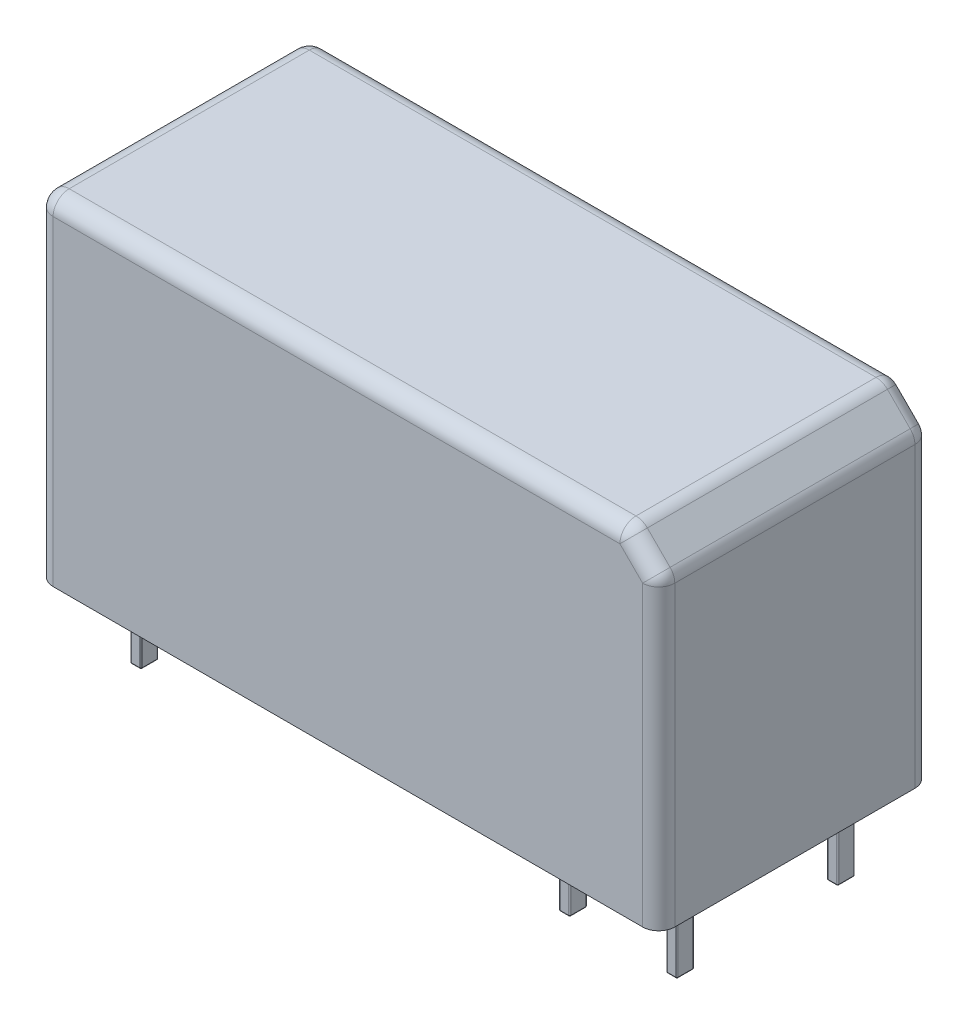
SolidWorks part; units mm, degrees
ref_plane "Спереди" through (0, 0, 0) normal (0, 0, 1) x (1, 0, 0)
ref_plane "Сверху" through (0, 0, 0) normal (0, 1, 0) x (1, 0, 0)
ref_plane "Справа" through (0, 0, 0) normal (1, 0, 0) x (0, 0, -1)
sketch "Эскиз1" plane through (0, 0, 0) normal (0, 1, 0) x (1, 0, 0)
  line L1 (-14.5, -6.35) -> (14.5, -6.35)
  line L2 (-14.5, -6.35) -> (-14.5, 6.35)
  line L3 (-14.5, 6.35) -> (14.5, 6.35)
  line L4 (14.5, -6.35) -> (14.5, 6.35)
  line L5 (-14.5, -6.35) -> (14.5, 6.35) construction
  line L6 (-14.5, 6.35) -> (14.5, -6.35) construction
  point P0 (0, 0)
  dimension "D1" = 29
  dimension "D2" = 12.7
extrude "Бобышка-Вытянуть1" add sketch "Эскиз1" along normal blind 15.7
sketch "Эскиз2" plane through (0, 0, 0) normal (0, -1, 0) x (1, 0, 0)
  line L0 (-14.5, -6.35) -> (-14.5, 6.35) construction
  line L1 (-12.3, 4.15) -> (-11.9, 4.15)
  line L2 (-12.35, 4.1) -> (-12.35, 3.4)
  line L3 (-12.3, 3.35) -> (-11.9, 3.35)
  line L4 (-11.85, 4.1) -> (-11.85, 3.4)
  line L5 (-12.35, 4.15) -> (-11.85, 3.35) construction
  line L6 (-12.35, 3.35) -> (-11.85, 4.15) construction
  line L7 (-7.35, 4.1) -> (-7.35, 3.4) [skipped]
  line L8 (-6.85, 4.1) -> (-6.85, 3.4) [skipped]
  line L9 (-7.3, 4.15) -> (-6.9, 4.15) [skipped]
  line L10 (-7.3, 3.35) -> (-6.9, 3.35) [skipped]
  line L11 (-2.35, 4.1) -> (-2.35, 3.4) [skipped]
  line L12 (-1.85, 4.1) -> (-1.85, 3.4) [skipped]
  line L13 (-2.3, 4.15) -> (-1.9, 4.15) [skipped]
  line L14 (-2.3, 3.35) -> (-1.9, 3.35) [skipped]
  line L19 (7.65, 4.1) -> (7.65, 3.4)
  line L20 (8.15, 4.1) -> (8.15, 3.4)
  line L21 (7.7, 4.15) -> (8.1, 4.15)
  line L22 (7.7, 3.35) -> (8.1, 3.35)
  line L23 (12.65, 4.1) -> (12.65, 3.4)
  line L24 (13.15, 4.1) -> (13.15, 3.4)
  line L25 (12.7, 4.15) -> (13.1, 4.15)
  line L26 (12.7, 3.35) -> (13.1, 3.35)
  line L27 (-7.35, -3.4) -> (-7.35, -4.1) [skipped]
  line L28 (-6.85, -3.4) -> (-6.85, -4.1) [skipped]
  line L29 (-7.3, -3.35) -> (-6.9, -3.35) [skipped]
  line L30 (-7.3, -4.15) -> (-6.9, -4.15) [skipped]
  line L31 (-2.35, -3.4) -> (-2.35, -4.1) [skipped]
  line L32 (-1.85, -3.4) -> (-1.85, -4.1) [skipped]
  line L33 (-2.3, -3.35) -> (-1.9, -3.35) [skipped]
  line L34 (-2.3, -4.15) -> (-1.9, -4.15) [skipped]
  line L39 (7.65, -3.4) -> (7.65, -4.1)
  line L40 (8.15, -3.4) -> (8.15, -4.1)
  line L41 (7.7, -3.35) -> (8.1, -3.35)
  line L42 (7.7, -4.15) -> (8.1, -4.15)
  line L43 (12.65, -3.4) -> (12.65, -4.1)
  line L44 (13.15, -3.4) -> (13.15, -4.1)
  line L45 (12.7, -3.35) -> (13.1, -3.35)
  line L46 (12.7, -4.15) -> (13.1, -4.15)
  line L47 (-12.35, -3.4) -> (-12.35, -4.1)
  line L48 (-11.85, -3.4) -> (-11.85, -4.1)
  line L49 (-12.3, -3.35) -> (-11.9, -3.35)
  line L50 (-12.3, -4.15) -> (-11.9, -4.15)
  line L51 (2.65, 4.1) -> (2.65, 3.4) [skipped]
  line L52 (3.15, 4.1) -> (3.15, 3.4) [skipped]
  line L53 (2.7, 4.15) -> (3.1, 4.15) [skipped]
  line L54 (2.7, 3.35) -> (3.1, 3.35) [skipped]
  line L55 (2.65, -3.4) -> (2.65, -4.1) [skipped]
  line L56 (3.15, -3.4) -> (3.15, -4.1) [skipped]
  line L57 (2.7, -3.35) -> (3.1, -3.35) [skipped]
  line L58 (2.7, -4.15) -> (3.1, -4.15) [skipped]
  arc A0 (-12.35, 3.4) -> (-12.3, 3.35) centre (-12.3, 3.4) ccw
  arc A1 (-11.9, 3.35) -> (-11.85, 3.4) centre (-11.9, 3.4) ccw
  arc A2 (-11.9, 4.15) -> (-11.85, 4.1) centre (-11.9, 4.1) cw
  arc A3 (-12.3, 4.15) -> (-12.35, 4.1) centre (-12.3, 4.1) ccw
  arc A4 (-7.35, 3.4) -> (-7.3, 3.35) centre (-7.3, 3.4) ccw [skipped]
  arc A5 (-6.9, 3.35) -> (-6.85, 3.4) centre (-6.9, 3.4) ccw [skipped]
  arc A6 (-6.9, 4.15) -> (-6.85, 4.1) centre (-6.9, 4.1) cw [skipped]
  arc A7 (-7.3, 4.15) -> (-7.35, 4.1) centre (-7.3, 4.1) ccw [skipped]
  arc A8 (-2.35, 3.4) -> (-2.3, 3.35) centre (-2.3, 3.4) ccw [skipped]
  arc A9 (-1.9, 3.35) -> (-1.85, 3.4) centre (-1.9, 3.4) ccw [skipped]
  arc A10 (-1.9, 4.15) -> (-1.85, 4.1) centre (-1.9, 4.1) cw [skipped]
  arc A11 (-2.3, 4.15) -> (-2.35, 4.1) centre (-2.3, 4.1) ccw [skipped]
  arc A16 (7.65, 3.4) -> (7.7, 3.35) centre (7.7, 3.4) ccw
  arc A17 (8.1, 3.35) -> (8.15, 3.4) centre (8.1, 3.4) ccw
  arc A18 (8.1, 4.15) -> (8.15, 4.1) centre (8.1, 4.1) cw
  arc A19 (7.7, 4.15) -> (7.65, 4.1) centre (7.7, 4.1) ccw
  arc A20 (12.65, 3.4) -> (12.7, 3.35) centre (12.7, 3.4) ccw
  arc A21 (13.1, 3.35) -> (13.15, 3.4) centre (13.1, 3.4) ccw
  arc A22 (13.1, 4.15) -> (13.15, 4.1) centre (13.1, 4.1) cw
  arc A23 (12.7, 4.15) -> (12.65, 4.1) centre (12.7, 4.1) ccw
  arc A24 (-7.35, -4.1) -> (-7.3, -4.15) centre (-7.3, -4.1) ccw [skipped]
  arc A25 (-6.9, -4.15) -> (-6.85, -4.1) centre (-6.9, -4.1) ccw [skipped]
  arc A26 (-6.9, -3.35) -> (-6.85, -3.4) centre (-6.9, -3.4) cw [skipped]
  arc A27 (-7.3, -3.35) -> (-7.35, -3.4) centre (-7.3, -3.4) ccw [skipped]
  arc A28 (-2.35, -4.1) -> (-2.3, -4.15) centre (-2.3, -4.1) ccw [skipped]
  arc A29 (-1.9, -4.15) -> (-1.85, -4.1) centre (-1.9, -4.1) ccw [skipped]
  arc A30 (-1.9, -3.35) -> (-1.85, -3.4) centre (-1.9, -3.4) cw [skipped]
  arc A31 (-2.3, -3.35) -> (-2.35, -3.4) centre (-2.3, -3.4) ccw [skipped]
  arc A36 (7.65, -4.1) -> (7.7, -4.15) centre (7.7, -4.1) ccw
  arc A37 (8.1, -4.15) -> (8.15, -4.1) centre (8.1, -4.1) ccw
  arc A38 (8.1, -3.35) -> (8.15, -3.4) centre (8.1, -3.4) cw
  arc A39 (7.7, -3.35) -> (7.65, -3.4) centre (7.7, -3.4) ccw
  arc A40 (12.65, -4.1) -> (12.7, -4.15) centre (12.7, -4.1) ccw
  arc A41 (13.1, -4.15) -> (13.15, -4.1) centre (13.1, -4.1) ccw
  arc A42 (13.1, -3.35) -> (13.15, -3.4) centre (13.1, -3.4) cw
  arc A43 (12.7, -3.35) -> (12.65, -3.4) centre (12.7, -3.4) ccw
  arc A44 (-12.35, -4.1) -> (-12.3, -4.15) centre (-12.3, -4.1) ccw
  arc A45 (-11.9, -4.15) -> (-11.85, -4.1) centre (-11.9, -4.1) ccw
  arc A46 (-11.9, -3.35) -> (-11.85, -3.4) centre (-11.9, -3.4) cw
  arc A47 (-12.3, -3.35) -> (-12.35, -3.4) centre (-12.3, -3.4) ccw
  arc A48 (2.65, 3.4) -> (2.7, 3.35) centre (2.7, 3.4) ccw [skipped]
  arc A49 (3.1, 3.35) -> (3.15, 3.4) centre (3.1, 3.4) ccw [skipped]
  arc A50 (3.1, 4.15) -> (3.15, 4.1) centre (3.1, 4.1) cw [skipped]
  arc A51 (2.7, 4.15) -> (2.65, 4.1) centre (2.7, 4.1) ccw [skipped]
  arc A52 (2.65, -4.1) -> (2.7, -4.15) centre (2.7, -4.1) ccw [skipped]
  arc A53 (3.1, -4.15) -> (3.15, -4.1) centre (3.1, -4.1) ccw [skipped]
  arc A54 (3.1, -3.35) -> (3.15, -3.4) centre (3.1, -3.4) cw [skipped]
  arc A55 (2.7, -3.35) -> (2.65, -3.4) centre (2.7, -3.4) ccw [skipped]
  point P0 (-12.1, 3.75)
  point P8 (-14.5, 0)
  point P21 (-11.85, 3.75)
  dimension "D1" = 0.05
  dimension "D2" = 0.5
  dimension "D3" = 3.75
  dimension "D4" = 2.4
  dimension "D5" = 0.8
  dimension "D6" = 6
  dimension "D7" = 2
extrude "Бобышка-Вытянуть2" add sketch "Эскиз2" along normal blind 3.5
fillet "Скругление1" radius 0.05 48 edges at (-11.8646, -3.5, 3.3646) (-12.1, -3.5, 3.35) (-12.3354, -3.5, 3.3646) (-12.35, -3.5, 3.75) (-12.3354, -3.5, 4.1354) (-12.1, -3.5, 4.15) (-11.8646, -3.5, 4.1354) (-11.8646, -3.5, -4.1354) (-12.1, -3.5, -4.15) (-12.3354, -3.5, -4.1354) (-12.35, -3.5, -3.75) (-12.3354, -3.5, -3.3646) (-12.1, -3.5, -3.35) (-11.8646, -3.5, -3.3646) (13.1354, -3.5, 3.3646) (12.9, -3.5, 3.35) (12.6646, -3.5, 3.3646) (12.65, -3.5, 3.75) (12.6646, -3.5, 4.1354) (12.9, -3.5, 4.15) (13.1354, -3.5, 4.1354) (8.1354, -3.5, 3.3646) (7.9, -3.5, 3.35) (7.6646, -3.5, 3.3646) (7.65, -3.5, 3.75) (7.6646, -3.5, 4.1354) (7.9, -3.5, 4.15) (8.1354, -3.5, 4.1354) (8.1354, -3.5, -4.1354) (7.9, -3.5, -4.15) (7.6646, -3.5, -4.1354) (7.65, -3.5, -3.75) (7.6646, -3.5, -3.3646) (7.9, -3.5, -3.35) (8.1354, -3.5, -3.3646) (13.1354, -3.5, -4.1354) (12.9, -3.5, -4.15) (12.6646, -3.5, -4.1354) (12.65, -3.5, -3.75) (12.6646, -3.5, -3.3646) (12.9, -3.5, -3.35) (13.1354, -3.5, -3.3646) (-11.85, -3.5, 3.75) (-11.85, -3.5, -3.75) (13.15, -3.5, 3.75) (8.15, -3.5, 3.75) (8.15, -3.5, -3.75) (13.15, -3.5, -3.75)
chamfer "Фаска1" distance 1.5 angle 45 1 edges at (14.5, 15.7, 0)
fillet "Скругление2" radius 0.75 11 edges at (13.75, 14.95, -6.35) (-14.5, 7.85, 6.35) (-14.5, 7.85, -6.35) (14.5, 7.1, -6.35) (14.5, 7.1, 6.35) (13.75, 14.95, 6.35) (14.5, 14.2, 0) (13, 15.7, 0) (-0.75, 15.7, -6.35) (-14.5, 15.7, 0) (-0.75, 15.7, 6.35)
